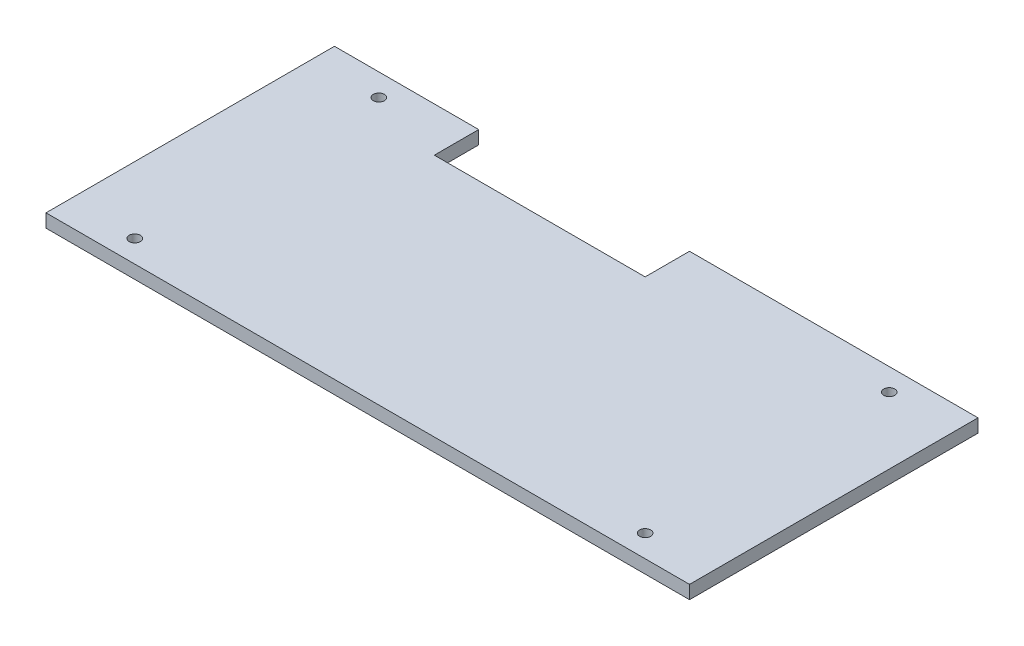
SolidWorks part; units mm, degrees
ref_plane "Front Plane" through (0, 0, 0) normal (0, 0, 1) x (1, 0, 0)
ref_plane "Top Plane" through (0, 0, 0) normal (0, 1, 0) x (1, 0, 0)
ref_plane "Right Plane" through (0, 0, 0) normal (1, 0, 0) x (0, 0, -1)
sketch "Sketch1" plane through (0, 0, 0) normal (0, 1, 0) x (1, 0, 0)
  line L0 (-160, -65) -> (130, -65)
  line L1 (130, -65) -> (130, 65)
  line L2 (130, 65) -> (0, 65)
  line L3 (0, 65) -> (0, 45)
  line L4 (0, 45) -> (-95, 45)
  line L5 (-95, 45) -> (-95, 65)
  line L6 (-95, 65) -> (-160, 65)
  line L7 (-160, 65) -> (-160, -65)
  circle A0 centre (-130, 55) radius 2.5
  circle A1 centre (100, 55) radius 2.5
  circle A2 centre (100, -55) radius 2.5
  circle A3 centre (-130, -55) radius 2.5
  point P7 (-160, 0)
  dimension "D6" = 5
  dimension "D1" = 130
  dimension "D2" = 20
  dimension "D3" = 95
  dimension "D4" = 65
  dimension "D5" = 290
  dimension "D7" = 10
  dimension "D8" = 10
  dimension "D9" = 30
  dimension "D10" = 30
extrude "Boss-Extrude1" add sketch "Sketch1" along normal blind 6
